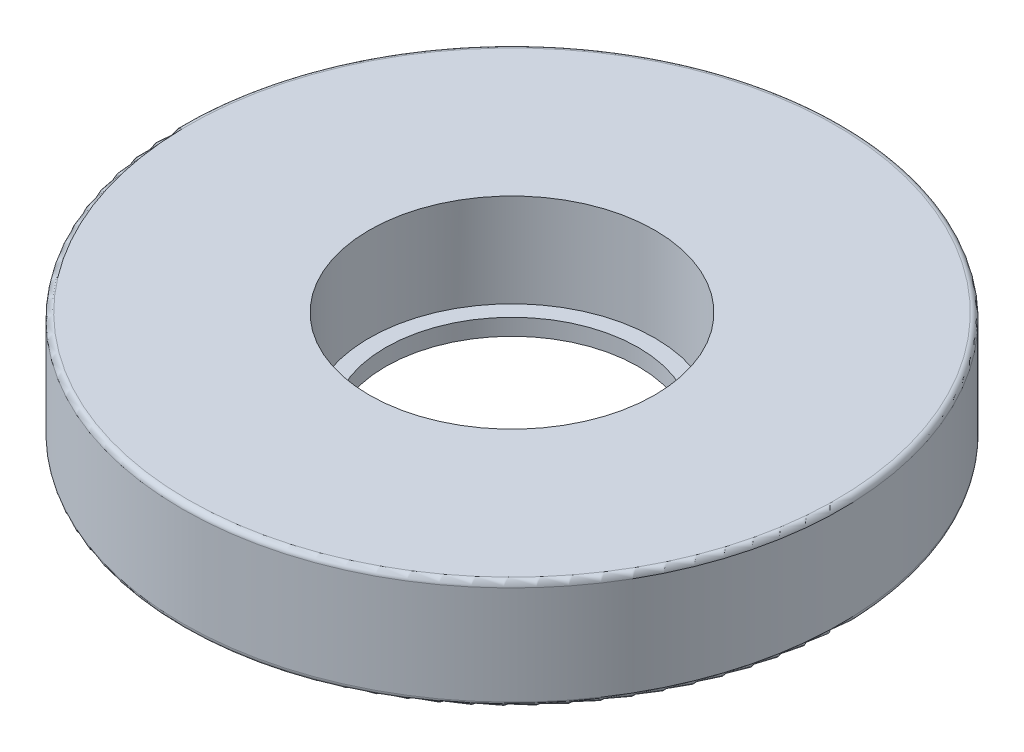
SolidWorks part; units mm, degrees
material "AISI 1045 钢，冷拔"
ref_plane "前视基准面" through (0, 0, 0) normal (0, 0, 1) x (1, 0, 0)
ref_plane "上视基准面" through (0, 0, 0) normal (0, 1, 0) x (1, 0, 0)
ref_plane "右视基准面" through (0, 0, 0) normal (1, 0, 0) x (0, 0, -1)
sketch "草图1" plane through (0, 0, 0) normal (0, 1, 0) x (1, 0, 0)
  circle A0 centre (0, 0) radius 60
  circle A1 centre (0, 0) radius 26
  dimension "D1" = 120
  dimension "D2" = 52
extrude "凸台-拉伸1" add sketch "草图1" along normal blind 20
fillet "圆角1" radius 1 2 edges at (0, 0, 60) (0, 20, 60)
sketch "草图2" plane through (0, 0, 0) normal (0, -1, 0) x (1, 0, 0)
  circle A0 centre (0, 0) radius 26
  circle A1 centre (0, 0) radius 23
  dimension "D1" = 52
  dimension "D2" = 46
extrude "凸台-拉伸2" add sketch "草图2" against normal blind 3
